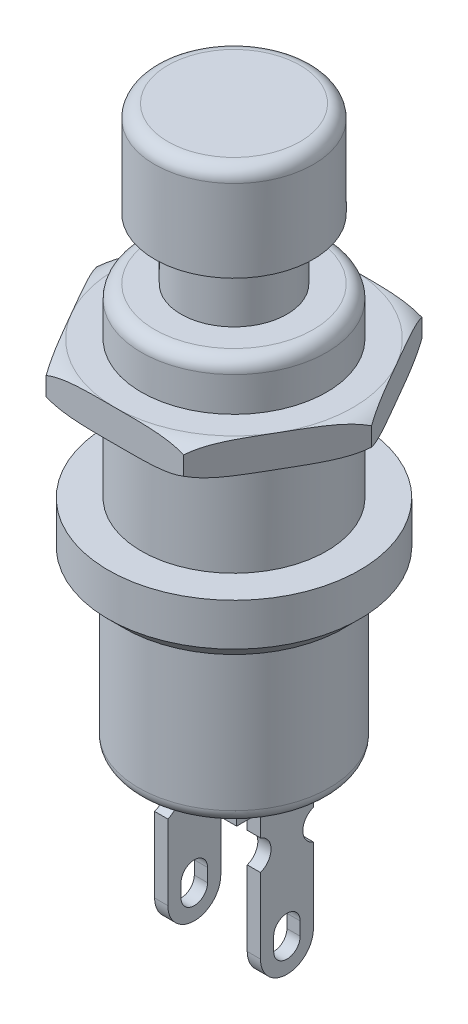
SolidWorks part; units mm, degrees
ref_plane "Front Plane" through (0, 0, 0) normal (0, 0, 1) x (1, 0, 0)
ref_plane "Top Plane" through (0, 0, 0) normal (0, 1, 0) x (1, 0, 0)
ref_plane "Right Plane" through (0, 0, 0) normal (1, 0, 0) x (0, 0, -1)
sketch "Sketch1" plane through (0, 0, 0) normal (0, 0, 1) x (1, 0, 0)
  line L0 (0, 0) -> (3.6, 0)
  line L1 (3.6, 0) -> (3.6, 6)
  line L2 (3.6, 6) -> (4.15, 6)
  line L3 (4.15, 6) -> (4.75, 6.6)
  line L4 (4.75, 6.6) -> (4.75, 8.2)
  line L5 (4.75, 8.2) -> (3.5, 8.2)
  line L6 (3.5, 8.2) -> (3.5, 15.2)
  line L7 (3.5, 15.2) -> (2, 15.2)
  line L8 (2, 15.2) -> (2, 17.5)
  line L9 (2, 17.5) -> (3, 17.5)
  line L10 (3, 17.5) -> (3, 21.1)
  line L11 (3, 21.1) -> (0, 21.1)
  line L12 (0, 21.1) -> (0, 0)
  dimension "D1" = 3
  dimension "D2" = 3.6
  dimension "D3" = 2.3
  dimension "D4" = 3.5
  dimension "D5" = 7
  dimension "D6" = 8.2
  dimension "D7" = 3.6
  dimension "D8" = 4.75
  dimension "D9" = 135
  dimension "D10" = 1.6
  dimension "D11" = 0.6
  dimension "D12" = 2
revolve "Revolve1" add sketch "Sketch1" angle 360 about L12
fillet "Fillet1" radius 0.5 3 edges at (-3.5, 15.2, 0) (-3, 21.1, 0) (-3.6, 0, 0)
sketch "Sketch2" plane through (0, 0, 0) normal (1, 0, 0) x (0, 0, -1)
  line L0 (-1.9, 0) -> (-1.9, -0.6)
  line L1 (-3.1, 0) -> (3.1, 0) construction
  line L2 (-1.9, -0.6) -> (-1, -0.6)
  line L3 (1, -5.4) -> (1, -0.6)
  line L4 (-1, -0.6) -> (-1, -5.4)
  line L5 (1, -0.6) -> (1.9, -0.6)
  line L6 (1.9, -0.6) -> (1.9, 0)
  line L7 (1.9, 0) -> (-1.9, 0)
  arc A0 (-1, -5.4) -> (1, -5.4) centre (0, -5.4) ccw
  dimension "D1" = 1
  dimension "D2" = 5.4
  dimension "D3" = 0.6
  dimension "D4" = 3.8
extrude "Boss-Extrude1" add sketch "Sketch2" along normal blind 0.5 from offset 1.5
sketch "Sketch3" plane through (2, 0, 0) normal (1, 0, 0) x (0, 0, -1)
  line L2 (0, -5.4) -> (0, -4.9) construction
  line L3 (-0.5, -5.4) -> (-0.5, -4.9)
  line L4 (0.5, -5.4) -> (0.5, -4.9)
  line L5 (-1, -0.6) -> (-1, -5.4) construction
  line L6 (1, -5.4) -> (1, -0.6) construction
  line L7 (1.9, 0) -> (-1.9, 0) construction
  circle A0 centre (-1.2, -2) radius 0.6
  circle A1 centre (1.2, -2) radius 0.6
  arc A2 (-0.5, -5.4) -> (0.5, -5.4) centre (0, -5.4) ccw
  arc A3 (0.5, -4.9) -> (-0.5, -4.9) centre (0, -4.9) ccw
  arc A5 (-1, -5.4) -> (1, -5.4) centre (0, -5.4) ccw construction
  point P11 (0, -5.15)
  dimension "D1" = 0.5
  dimension "D3" = 1.2
  dimension "D2" = 0.5
  dimension "D4" = 0.2
  dimension "D5" = 0.2
  dimension "D6" = 2
extrude "Cut-Extrude1" cut sketch "Sketch3" against normal up to next (0.5 mm away)
mirror "Mirror1" about plane through (0, 0, 0) normal (1, 0, 0) of "Cut-Extrude1", "Boss-Extrude1"
sketch "Sketch4" plane through (0, 8.2, 0) normal (0, 1, 0) x (1, 0, 0)
  line L1 (5.1962, 0) -> (2.5981, 4.5)
  line L2 (2.5981, 4.5) -> (-2.5981, 4.5)
  line L3 (-2.5981, 4.5) -> (-5.1962, 0)
  line L4 (-5.1962, 0) -> (-2.5981, -4.5)
  line L5 (-2.5981, -4.5) -> (2.5981, -4.5)
  line L6 (2.5981, -4.5) -> (5.1962, 0)
  circle A0 centre (0, 0) radius 4.5 construction
  circle A1 centre (0, 0) radius 3.5
  dimension "D1" = 9
extrude "Boss-Extrude2" add sketch "Sketch4" along normal blind 1.2 from offset 4
sketch "Sketch5" plane through (0, 0, 0) normal (0, 0, 1) x (1, 0, 0)
  line L0 (-5.1962, 13.4) -> (-4.5, 13.4)
  line L1 (-5.1962, 13.4) -> (-2.5981, 13.4) construction
  line L2 (-5.1962, 13.4) -> (-5.1962, 12.2) construction
  line L3 (-5.1962, 13.15) -> (-5.1962, 13.4)
  line L4 (-4.5, 12.2) -> (-5.1962, 12.2)
  line L5 (-5.1962, 12.2) -> (-2.5981, 12.2) construction
  line L6 (-5.1962, 12.2) -> (-5.1962, 12.45)
  line L7 (0, 13.4) -> (0, 12.2) construction
  line L8 (-2.5981, 13.4) -> (2.5981, 13.4) construction
  line L9 (-2.5981, 12.2) -> (2.5981, 12.2) construction
  arc A0 (-4.5, 13.4) -> (-5.1962, 13.15) centre (-4.5, 12.3057) ccw
  arc A1 (-5.1962, 12.45) -> (-4.5, 12.2) centre (-4.5, 13.2943) ccw
  dimension "D1" = 0.25
  dimension "D2" = 4.5
revolve "Cut-Revolve1" cut sketch "Sketch5" angle 360 about L7
